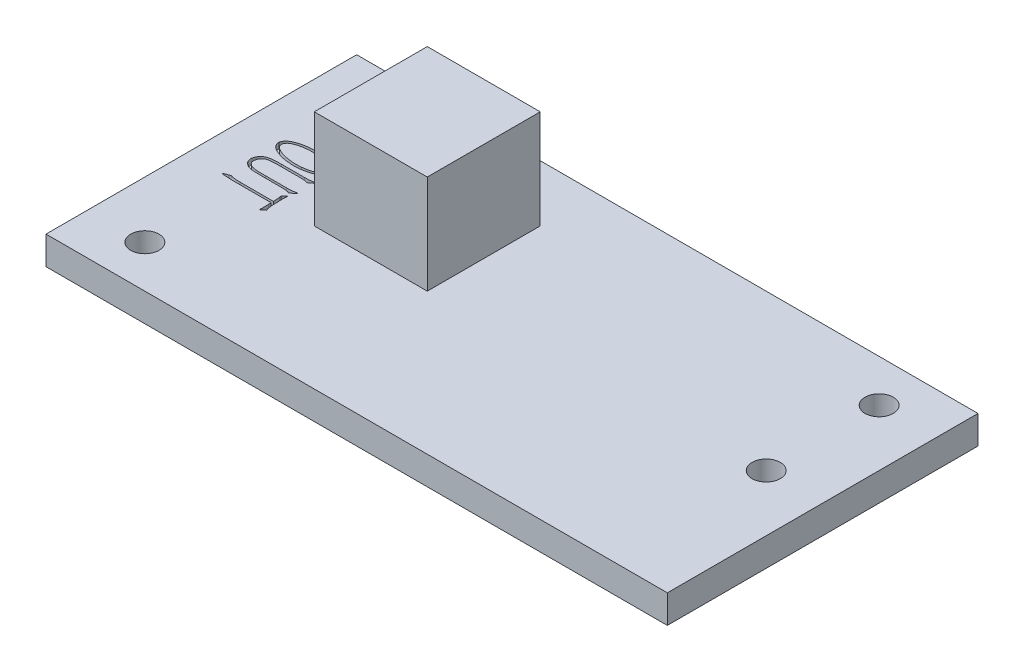
SolidWorks part; units mm, degrees
ref_plane "前视基准面" through (0, 0, 0) normal (0, 0, 1) x (1, 0, 0)
ref_plane "上视基准面" through (0, 0, 0) normal (0, 1, 0) x (1, 0, 0)
ref_plane "右视基准面" through (0, 0, 0) normal (1, 0, 0) x (0, 0, -1)
sketch "草图1" plane through (0, 0, 0) normal (0, 1, 0) x (1, 0, 0)
  line L1 (-11, 5.5) -> (11, 5.5)
  line L2 (-11, 5.5) -> (-11, -5.5)
  line L3 (-11, -5.5) -> (11, -5.5)
  line L4 (11, 5.5) -> (11, -5.5)
  line L5 (-11, 5.5) -> (11, -5.5) construction
  line L6 (-11, -5.5) -> (11, 5.5) construction
  point P0 (0, 0)
  dimension "D1" = 22
  dimension "D2" = 11
extrude "凸台-拉伸1" add sketch "草图1" along normal blind 1
sketch "草图2" plane through (0, 1, 0) normal (0, 1, 0) x (1, 0, 0)
  line L0 (11, 5.5) -> (-11, 5.5) construction
  line L1 (-6.5, 3.5) -> (-2.5, 3.5)
  line L2 (-6.5, 3.5) -> (-6.5, -0.5)
  line L3 (-6.5, -0.5) -> (-2.5, -0.5)
  line L4 (-2.5, 3.5) -> (-2.5, -0.5)
  line L5 (-11, 5.5) -> (-11, -5.5) construction
  dimension "D1" = 4
  dimension "D2" = 4
  dimension "D3" = 2
  dimension "D4" = 4.5
extrude "凸台-拉伸2" add sketch "草图2" along normal blind 4.5 from surface at -1 starting at face at (0, 0, 0)
sketch "草图3" plane through (0, 1, 0) normal (0, 1, 0) x (1, 0, 0)
  line L0 (11, -5.5) -> (11, 5.5) construction
  line L2 (11, 5.5) -> (-11, 5.5) construction
  line L3 (-11, 5.5) -> (-11, -5.5) construction
  line L4 (0, 0) -> (-11, 0) construction
  circle A0 centre (-9, 4) radius 0.5
  circle A2 centre (9, 4) radius 0.5
  circle A3 centre (9, 0) radius 0.5
  circle A4 centre (-9, -4) radius 0.5
  dimension "D1" = 1
  dimension "D2" = 2
  dimension "D3" = 1.5
  dimension "D4" = 1.5
  dimension "D5" = 2
  dimension "D6" = 4
extrude "切除-拉伸1" cut sketch "草图3" against normal through all
sketch "草图4" plane through (0, 1, 0) normal (0, 1, 0) x (1, 0, 0)
  line L0 (-9.8477, 1.8854) -> (-9.8477, -0.9896) construction
  text T0 "OUT" font "汉仪长仿宋体" height 2
extrude "切除-拉伸2" cut sketch "草图4" against normal blind 0.2
